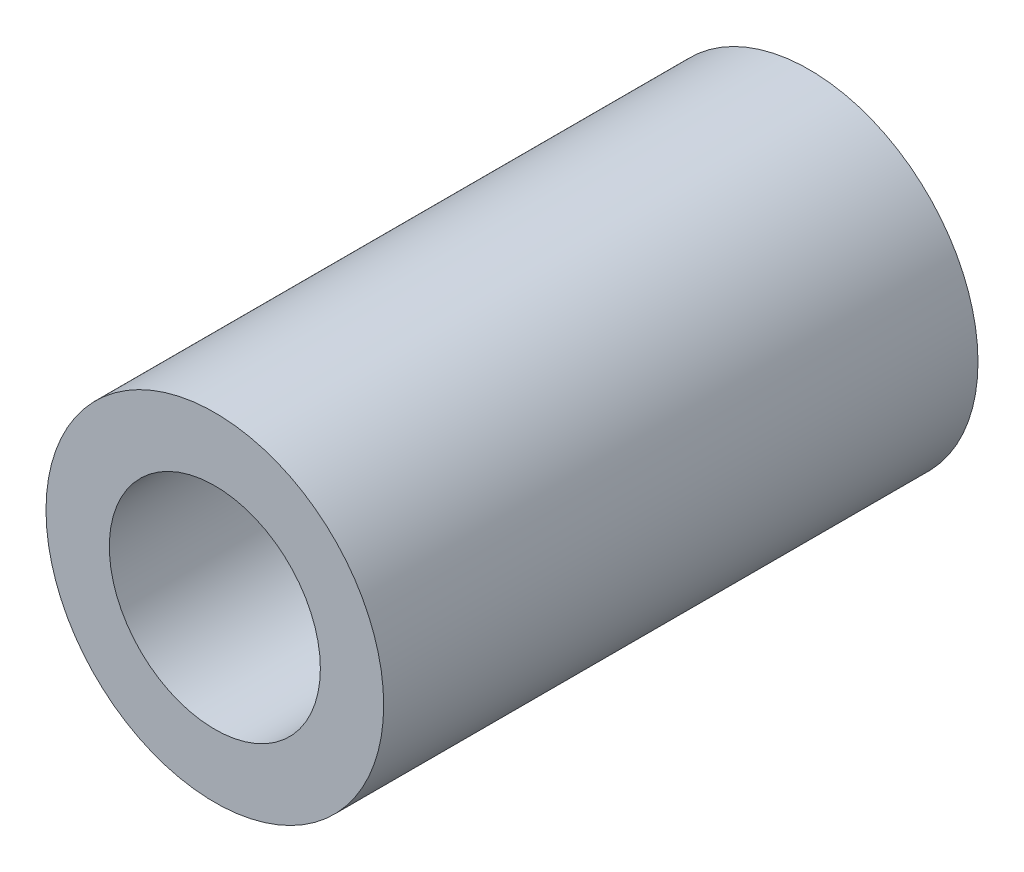
SolidWorks part; units mm, degrees
ref_plane "Front Plane" through (0, 0, 0) normal (0, 0, 1) x (1, 0, 0)
ref_plane "Top Plane" through (0, 0, 0) normal (0, 1, 0) x (1, 0, 0)
ref_plane "Right Plane" through (0, 0, 0) normal (1, 0, 0) x (0, 0, -1)
sketch "Sketch1" plane through (0, 0, 0) normal (0, 0, 1) x (1, 0, 0)
  circle A0 centre (0, 0) radius 1.5875
extrude "Boss-Extrude1" add sketch "Sketch1" along normal blind 5.588
sketch "Sketch3" plane through (0, 0, 5.588) normal (0, 0, 1) x (1, 0, 0)
  circle A0 centre (0, 0) radius 0.9922
extrude "Cut-Extrude1" cut sketch "Sketch3" against normal up to next
